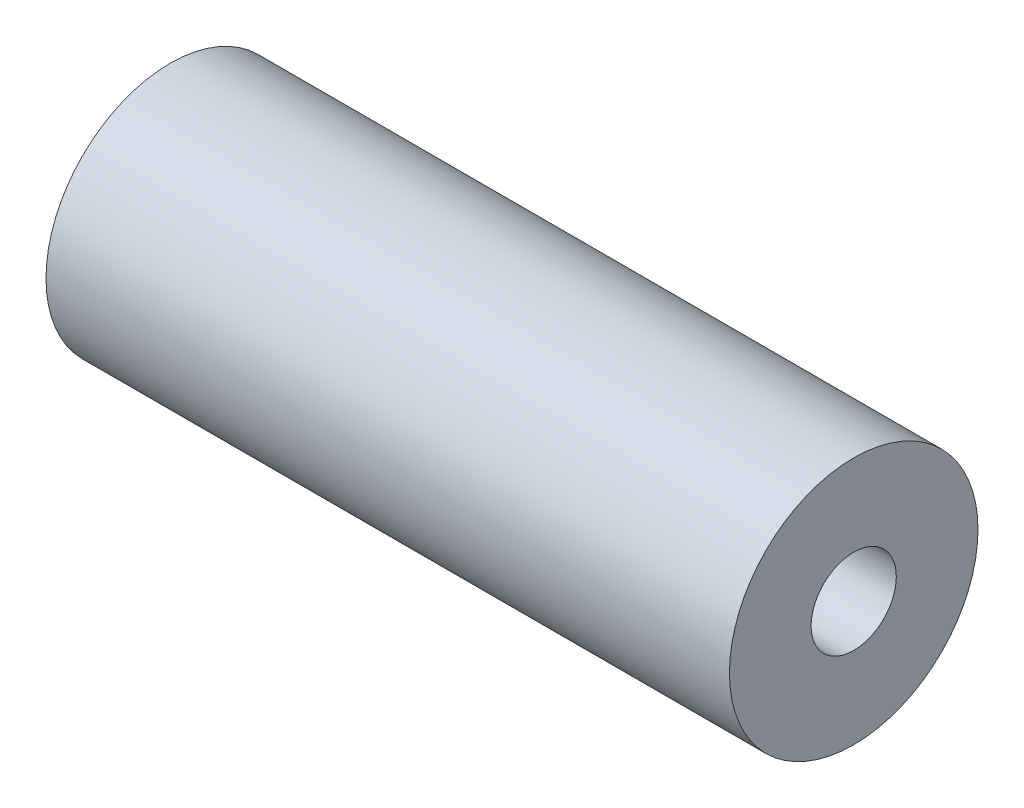
SolidWorks part; units mm, degrees
material "ABS"
ref_plane "Front Plane" through (0, 0, 0) normal (0, 0, 1) x (1, 0, 0)
ref_plane "Top Plane" through (0, 0, 0) normal (0, 1, 0) x (1, 0, 0)
ref_plane "Right Plane" through (0, 0, 0) normal (1, 0, 0) x (0, 0, -1)
sketch "Sketch1" plane through (0, 0, 0) normal (1, 0, 0) x (0, 0, -1)
  circle A0 centre (0, 0) radius 9.525
  circle A1 centre (0, 0) radius 3.2639
  dimension "D1" = 19.05
  dimension "D2" = 6.5278
extrude "Boss-Extrude1" add sketch "Sketch1" along normal blind 52.3875
